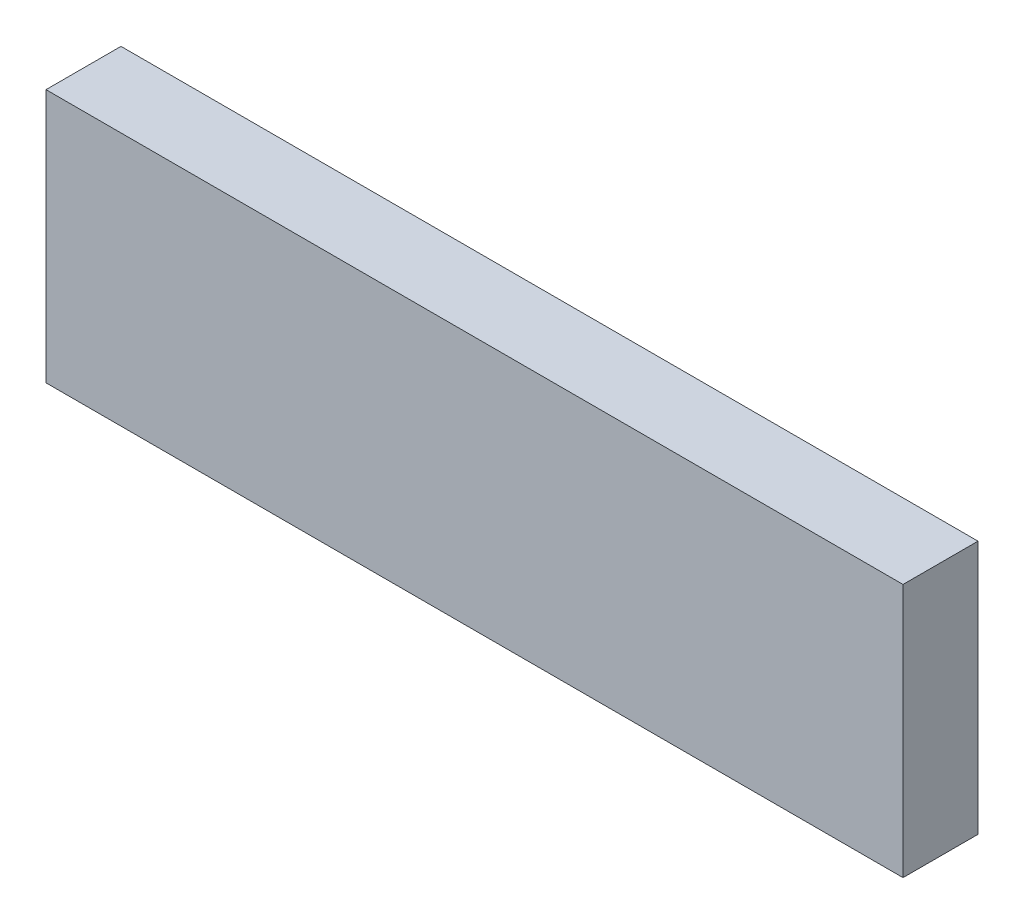
SolidWorks part; units mm, degrees
ref_plane "Front Plane" through (0, 0, 0) normal (0, 0, 1) x (1, 0, 0)
ref_plane "Top Plane" through (0, 0, 0) normal (0, 1, 0) x (1, 0, 0)
ref_plane "Right Plane" through (0, 0, 0) normal (1, 0, 0) x (0, 0, -1)
sketch "Sketch1" plane through (0, 0, 0) normal (0, 0, 1) x (1, 0, 0)
  line L0 (-34.29, 10.16) -> (0, 10.16)
  line L1 (-34.29, 10.16) -> (-34.29, 0)
  line L2 (-34.29, 0) -> (0, 0)
  line L3 (0, 10.16) -> (0, 0)
  point P4 (-34.29, 5.08)
  dimension "D1" = 0
extrude "Boss-Extrude1" add sketch "Sketch1" along normal blind 3
